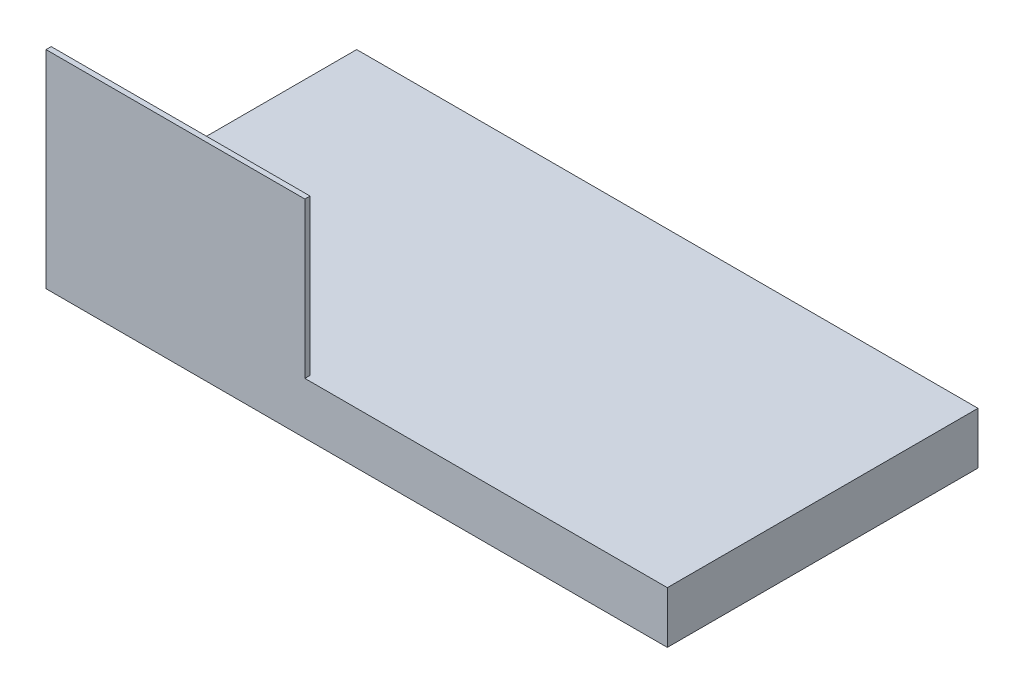
SolidWorks part; units mm, degrees
ref_plane "Front Plane" through (0, 0, 0) normal (0, 0, 1) x (1, 0, 0)
ref_plane "Top Plane" through (0, 0, 0) normal (0, 1, 0) x (1, 0, 0)
ref_plane "Right Plane" through (0, 0, 0) normal (1, 0, 0) x (0, 0, -1)
sketch "Sketch1" plane through (0, 0, 0) normal (0, 1, 0) x (1, 0, 0)
  line L1 (60, 30) -> (-60, 30)
  line L2 (60, 30) -> (60, -30)
  line L3 (60, -30) -> (-60, -30)
  line L4 (-60, 30) -> (-60, -30)
  line L5 (60, 30) -> (-60, -30) construction
  line L6 (60, -30) -> (-60, 30) construction
  point P0 (0, 0)
  dimension "D1" = 60
  dimension "D2" = 120
extrude "Boss-Extrude1" add sketch "Sketch1" along normal blind 10
sketch "Sketch2" plane through (0, 10, 0) normal (0, 1, 0) x (1, 0, 0)
  line L0 (-60, -30) -> (-10, -30)
  line L1 (-60, -30) -> (60, -30) construction
  line L6 (-60, 30) -> (-60, -30)
  line L7 (-60, -30) -> (60, -30)
  line L8 (60, -30) -> (60, 30)
  line L9 (60, 30) -> (-60, 30)
  line L11 (-60, -30) -> (-10, -30)
  dimension "D1" = 50
  dimension "D2" = 0
sketch "Sketch3" plane through (0, 10, 0) normal (0, 1, 0) x (1, 0, 0)
  line L0 (-60, -30) -> (-10, -30)
  line L1 (-60, -30) -> (60, -30) construction
  dimension "D1" = 50
extrude "Extrude-Thin4" add sketch "Sketch3" along normal blind 30 thin thin type one direction reverse wall 1
